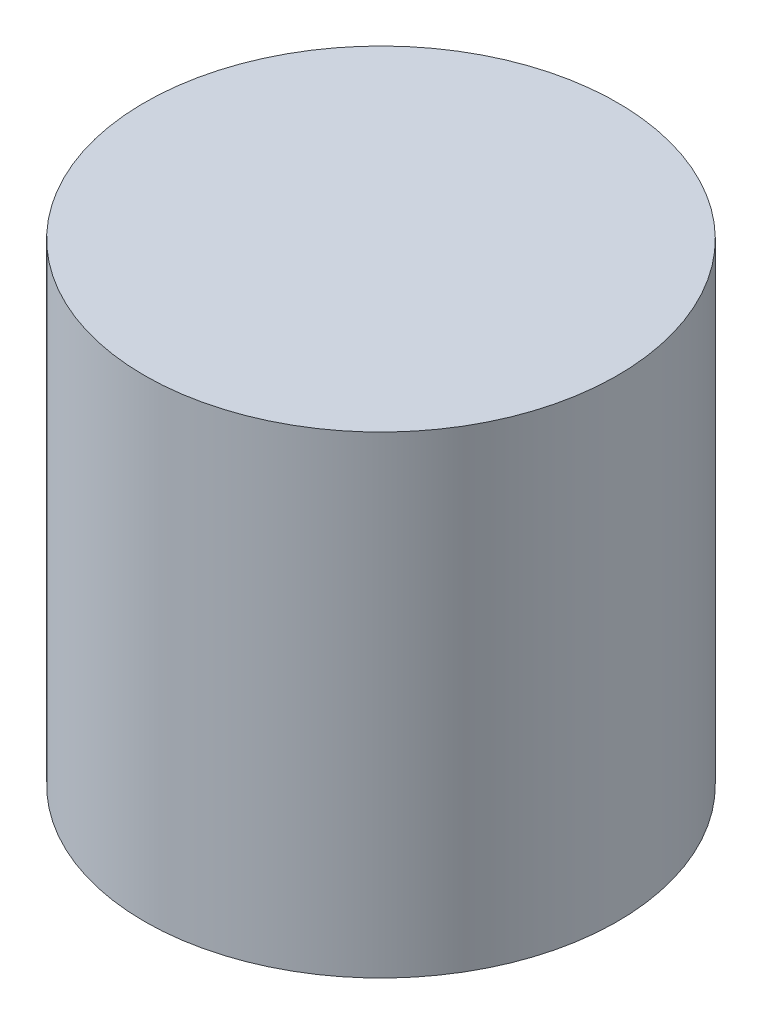
SolidWorks part; units mm, degrees
ref_plane "Front Plane" through (0, 0, 0) normal (0, 0, 1) x (1, 0, 0)
ref_plane "Top Plane" through (0, 0, 0) normal (0, 1, 0) x (1, 0, 0)
ref_plane "Right Plane" through (0, 0, 0) normal (1, 0, 0) x (0, 0, -1)
sketch "Sketch1" plane through (0, 0, 0) normal (0, 1, 0) x (1, 0, 0)
  circle A0 centre (0, 0) radius 5
  dimension "D1" = 10
extrude "Boss-Extrude1" add sketch "Sketch1" along normal blind 10
